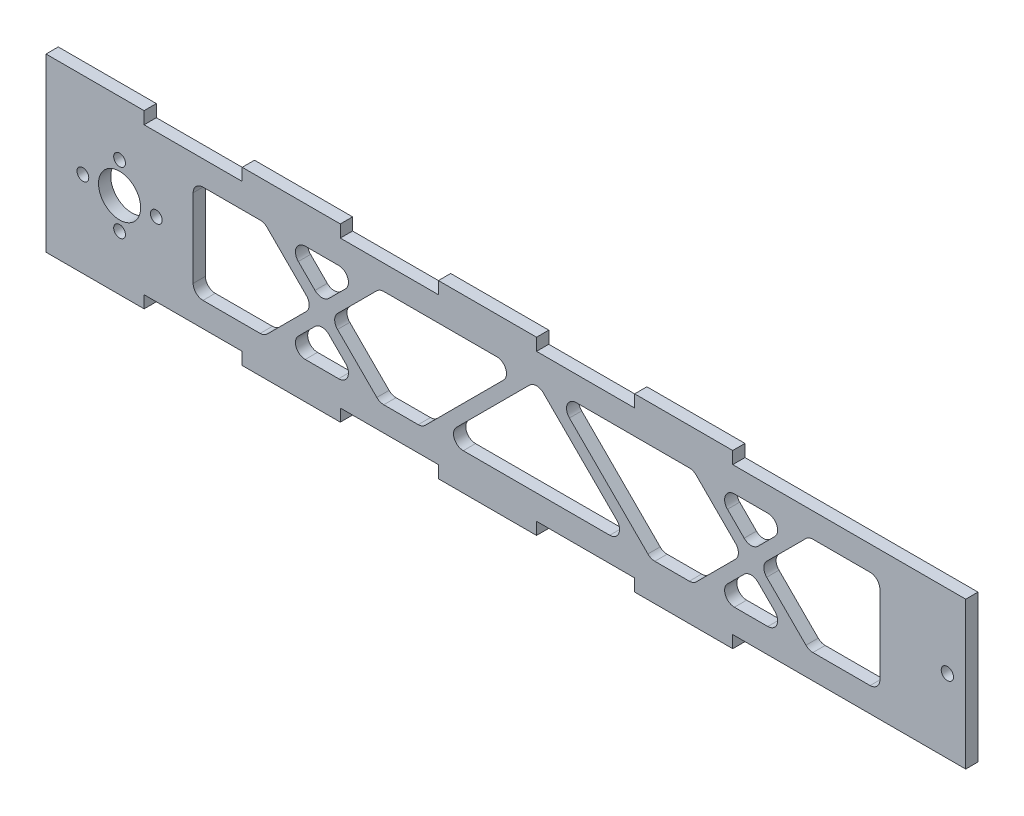
SolidWorks part; units mm, degrees
material "ABS"
ref_plane "Front Plane" through (0, 0, 0) normal (0, 0, 1) x (1, 0, 0)
ref_plane "Top Plane" through (0, 0, 0) normal (0, 1, 0) x (1, 0, 0)
ref_plane "Right Plane" through (0, 0, 0) normal (1, 0, 0) x (0, 0, -1)
sketch "Sketch1" plane through (0, 0, 0) normal (0, 0, 1) x (1, 0, 0)
  line L0 (-24.8893, 17.42) -> (0.5107, 17.42)
  line L1 (-75.6893, 17.42) -> (-50.2893, 17.42)
  line L2 (-75.6893, 17.42) -> (-75.6893, -27.03)
  line L3 (-2.4489, -0.7639) -> (1.8739, 3.5589)
  line L4 (152.9107, 14.245) -> (162.4357, 14.245)
  line L5 (-50.2893, 14.245) -> (-50.2893, 17.42)
  line L6 (-50.2893, 14.245) -> (-24.8893, 14.245)
  line L7 (-24.8893, 14.245) -> (-24.8893, 17.42)
  line L8 (0.5107, 14.245) -> (0.5107, 17.42)
  line L9 (0.5107, 14.245) -> (25.9107, 14.245)
  line L10 (25.9107, 14.245) -> (25.9107, 17.42)
  line L11 (25.9107, 17.42) -> (51.3107, 17.42)
  line L12 (51.3107, 14.245) -> (51.3107, 17.42)
  line L13 (51.3107, 14.245) -> (76.7107, 14.245)
  line L14 (76.7107, 14.245) -> (76.7107, 17.42)
  line L15 (76.7107, 17.42) -> (102.1107, 17.42)
  line L16 (102.1107, 14.245) -> (102.1107, 17.42)
  line L17 (102.1107, 14.245) -> (152.9107, 14.245)
  line L18 (162.4357, 14.245) -> (162.4357, -23.855)
  line L19 (152.9107, 14.245) -> (152.9107, -23.855) construction
  line L20 (157.6732, 14.245) -> (157.6732, -23.855) construction
  line L22 (102.1107, -23.855) -> (162.4357, -23.855)
  line L23 (152.9107, 14.245) -> (178.3107, 14.245) [skipped]
  line L24 (178.3107, 14.245) -> (178.3107, 17.42) [skipped]
  line L25 (152.9107, 14.245) -> (152.9107, 17.42) [skipped]
  line L26 (102.1107, -23.855) -> (102.1107, -27.03)
  line L27 (76.7107, -27.03) -> (102.1107, -27.03)
  line L28 (76.7107, -23.855) -> (76.7107, -27.03)
  line L29 (51.3107, -23.855) -> (76.7107, -23.855)
  line L30 (51.3107, -23.855) -> (51.3107, -27.03)
  line L31 (25.9107, -27.03) -> (51.3107, -27.03)
  line L32 (25.9107, -23.855) -> (25.9107, -27.03)
  line L33 (0.5107, -23.855) -> (25.9107, -23.855)
  line L34 (0.5107, -23.855) -> (0.5107, -27.03)
  line L35 (-24.8893, -23.855) -> (-24.8893, -27.03)
  line L36 (-50.2893, -23.855) -> (-24.8893, -23.855)
  line L37 (-50.2893, -23.855) -> (-50.2893, -27.03)
  line L38 (-75.6893, -27.03) -> (-50.2893, -27.03)
  line L39 (-24.8893, -27.03) -> (0.5107, -27.03)
  line L40 (-8.5678, -17.505) -> (0.0779, -17.505)
  line L41 (-37.5893, 5.355) -> (-37.5893, -14.965)
  line L42 (9.9562, 7.151) -> (-0.2038, -3.009)
  line L43 (-35.0493, 7.895) -> (-20.2421, 7.895)
  line L44 (-6.041, -8.8461) -> (-10.3638, -13.169)
  line L45 (11.7522, 7.895) -> (40.9976, 7.895)
  line L46 (-20.2421, -17.505) -> (-35.0493, -17.505)
  line L47 (22.4736, -16.7611) -> (42.7936, 3.5589)
  line L48 (-18.4461, 7.151) -> (-8.2861, -3.009)
  line L49 (-6.041, -0.7639) -> (-10.3638, 3.5589)
  line L50 (-18.4461, -16.7611) -> (-8.2861, -6.6011)
  line L51 (9.9562, -16.7611) -> (-0.2038, -6.6011)
  line L52 (-2.4489, -8.8461) -> (1.8739, -13.169)
  line L53 (-8.5678, 7.895) -> (0.0779, 7.895)
  line L54 (11.7522, -17.505) -> (20.6776, -17.505)
  line L56 (121.0675, -16.7611) -> (110.9075, -6.6011)
  line L57 (121.0675, 7.151) -> (110.9075, -3.009)
  line L58 (137.6707, 7.895) -> (122.8635, 7.895)
  line L59 (140.2107, 5.355) -> (140.2107, -14.965)
  line L60 (122.8635, -17.505) -> (137.6707, -17.505)
  line L61 (90.8692, 7.895) -> (61.6238, 7.895)
  line L62 (92.6653, 7.151) -> (102.8253, -3.009)
  line L63 (92.6653, -16.7611) -> (102.8253, -6.6011)
  line L64 (90.8692, -17.505) -> (81.9438, -17.505)
  line L65 (80.1478, -16.7611) -> (59.8278, 3.5589)
  line L66 (111.1892, -17.505) -> (102.5435, -17.505)
  line L67 (108.6624, -8.8461) -> (112.9853, -13.169)
  line L68 (105.0703, -8.8461) -> (100.7475, -13.169)
  line L69 (105.0703, -0.7639) -> (100.7475, 3.5589)
  line L70 (111.1892, 7.895) -> (102.5435, 7.895)
  line L71 (108.6624, -0.7639) -> (112.9853, 3.5589)
  line L73 (67.7427, -8.8461) -> (72.0655, -13.169)
  line L74 (67.7427, -8.8461) -> (53.1068, 5.7898)
  line L76 (30.5559, -13.169) -> (49.5147, 5.7898)
  line L77 (32.3519, -17.505) -> (70.2695, -17.505)
  line L78 (127.5107, 17.42) -> (152.9107, 17.42) [skipped]
  line L79 (127.5107, 14.245) -> (127.5107, 17.42) [skipped]
  circle A0 centre (-47.1397, -4.805) radius 1.524
  circle A1 centre (-56.6393, -12.806) radius 1.524
  circle A2 centre (-56.6393, 3.196) radius 1.524
  arc A3 (121.0675, -16.7611) -> (122.8635, -17.505) centre (122.8635, -14.965) ccw
  arc A4 (20.6776, -17.505) -> (22.4736, -16.7611) centre (20.6776, -14.965) ccw
  arc A5 (-8.5678, -17.505) -> (-10.3638, -13.169) centre (-8.5678, -14.965) cw
  arc A6 (9.9562, 7.151) -> (11.7522, 7.895) centre (11.7522, 5.355) cw
  arc A7 (-37.5893, 5.355) -> (-35.0493, 7.895) centre (-35.0493, 5.355) cw
  arc A8 (42.7936, 3.5589) -> (40.9976, 7.895) centre (40.9976, 5.355) ccw
  arc A9 (-35.0493, -17.505) -> (-37.5893, -14.965) centre (-35.0493, -14.965) cw
  arc A10 (-18.4461, -16.7611) -> (-20.2421, -17.505) centre (-20.2421, -14.965) cw
  arc A11 (-18.4461, 7.151) -> (-20.2421, 7.895) centre (-20.2421, 5.355) ccw
  arc A12 (1.8739, 3.5589) -> (0.0779, 7.895) centre (0.0779, 5.355) ccw
  arc A13 (-10.3638, 3.5589) -> (-8.5678, 7.895) centre (-8.5678, 5.355) cw
  arc A14 (-2.4489, -0.7639) -> (-6.041, -0.7639) centre (-4.245, 1.0322) cw
  arc A15 (-8.2861, -6.6011) -> (-8.2861, -3.009) centre (-10.0821, -4.805) ccw
  arc A16 (-2.4489, -8.8461) -> (-6.041, -8.8461) centre (-4.245, -10.6422) ccw
  arc A17 (-0.2038, -6.6011) -> (-0.2038, -3.009) centre (1.5922, -4.805) cw
  arc A18 (11.7522, -17.505) -> (9.9562, -16.7611) centre (11.7522, -14.965) cw
  arc A19 (0.0779, -17.505) -> (1.8739, -13.169) centre (0.0779, -14.965) ccw
  circle A20 centre (-66.1389, -4.805) radius 1.524
  arc A21 (110.9075, -6.6011) -> (110.9075, -3.009) centre (112.7035, -4.805) cw
  arc A22 (121.0675, 7.151) -> (122.8635, 7.895) centre (122.8635, 5.355) cw
  arc A23 (140.2107, 5.355) -> (137.6707, 7.895) centre (137.6707, 5.355) ccw
  arc A24 (137.6707, -17.505) -> (140.2107, -14.965) centre (137.6707, -14.965) ccw
  arc A25 (59.8278, 3.5589) -> (61.6238, 7.895) centre (61.6238, 5.355) cw
  arc A26 (92.6653, 7.151) -> (90.8692, 7.895) centre (90.8692, 5.355) ccw
  arc A27 (102.8253, -6.6011) -> (102.8253, -3.009) centre (101.0292, -4.805) ccw
  arc A28 (90.8692, -17.505) -> (92.6653, -16.7611) centre (90.8692, -14.965) ccw
  arc A29 (81.9438, -17.505) -> (80.1478, -16.7611) centre (81.9438, -14.965) cw
  arc A30 (102.5435, -17.505) -> (100.7475, -13.169) centre (102.5435, -14.965) cw
  arc A31 (111.1892, -17.505) -> (112.9853, -13.169) centre (111.1892, -14.965) ccw
  arc A32 (105.0703, -8.8461) -> (108.6624, -8.8461) centre (106.8664, -10.6422) cw
  arc A33 (105.0703, -0.7639) -> (108.6624, -0.7639) centre (106.8664, 1.0322) ccw
  arc A34 (100.7475, 3.5589) -> (102.5435, 7.895) centre (102.5435, 5.355) cw
  arc A35 (112.9853, 3.5589) -> (111.1892, 7.895) centre (111.1892, 5.355) ccw
  arc A36 (53.1068, 5.7898) -> (49.5147, 5.7898) centre (51.3107, 3.9938) ccw
  arc A37 (70.2695, -17.505) -> (72.0655, -13.169) centre (70.2695, -14.965) ccw
  arc A38 (32.3519, -17.505) -> (30.5559, -13.169) centre (32.3519, -14.965) cw
  circle A39 centre (157.6732, -4.805) radius 1.5875
  circle A40 centre (-56.6393, -4.805) radius 5.461
  point P87 (-14.6999, 7.895)
  point P90 (-4.245, -2.5599)
  point P95 (-4.245, -7.0501)
  point P100 (10.7001, -17.505)
  point P163 (26.2198, -17.505)
  dimension "D7" = 9.525
  dimension "D8" = 3.048
  dimension "D9" = 3.175
  dimension "D10" = 10.922
  dimension "D11" = 2.54
  dimension "D12" = 2.54
  dimension "D13" = 2.54
  dimension "D16" = 3.048
  dimension "D6" = 3.048
  dimension "D4" = 2.54
  dimension "D1" = 3.175
  dimension "D2" = 44.45
  dimension "D3" = 5
  dimension "D5" = 25.4
  dimension "D14" = 6.35
extrude "Boss-Extrude1" add sketch "Sketch1" along normal blind 3.175
sketch "Sketch2" plane through (0, 0, 3.175) normal (0, 0, 1) x (1, 0, 0)
  circle A1 centre (-56.6393, -4.805) radius 1.0258
